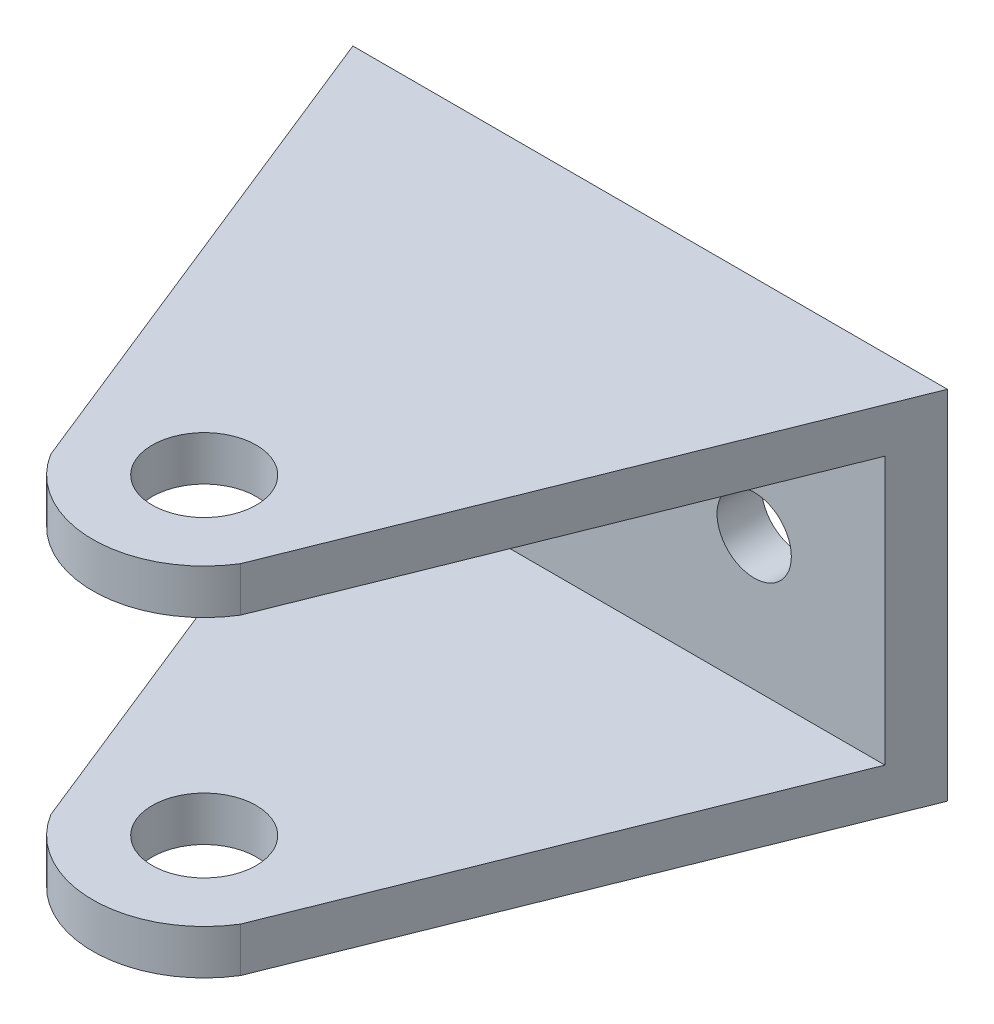
SolidWorks part; units mm, degrees
ref_plane "前视基准面" through (0, 0, 0) normal (0, 0, 1) x (1, 0, 0)
ref_plane "上视基准面" through (0, 0, 0) normal (0, 1, 0) x (1, 0, 0)
ref_plane "右视基准面" through (0, 0, 0) normal (1, 0, 0) x (0, 0, -1)
sketch "草图1" plane through (0, 0, 0) normal (0, 0, 1) x (1, 0, 0)
  line L0 (-29.7727, 16.3946) -> (-29.7727, -7.6054)
  line L1 (-29.7727, -7.6054) -> (0.2273, -7.6054)
  line L2 (0.2273, -7.6054) -> (10.2273, -7.6054)
  line L3 (10.2273, -7.6054) -> (10.2273, 16.3946)
  line L4 (-29.7727, 16.3946) -> (10.2273, 16.3946)
  line L5 (-29.7727, 4.3946) -> (-19.7727, 4.3946) construction
  line L6 (10.2273, 4.3946) -> (0.2273, 4.3946) construction
  circle A0 centre (-19.7727, 4.3946) radius 2.5
  circle A1 centre (0.2273, 4.3946) radius 2.5
  dimension "D5" = 5
  dimension "D6" = 10
  dimension "D7" = 5
  dimension "D1" = 24
  dimension "D2" = 30
  dimension "D3" = 10
  dimension "D4" = 10
extrude "凸台-拉伸1" add sketch "草图1" along normal blind 3
sketch "草图2" plane through (0, 0, 3) normal (0, 0, 1) x (1, 0, 0)
  line L0 (-29.7727, -7.6054) -> (-29.7727, -4.6054)
  line L1 (-29.7727, 16.3946) -> (-29.7727, -7.6054) construction
  line L2 (-29.7727, -4.6054) -> (10.2273, -4.6054)
  line L3 (10.2273, -7.6054) -> (10.2273, 16.3946) construction
  line L4 (10.2273, -4.6054) -> (10.2273, -7.6054)
  line L5 (10.2273, -7.6054) -> (-29.7727, -7.6054)
  line L6 (-29.7727, 16.3946) -> (-29.7727, 13.3946)
  line L7 (-29.7727, 13.3946) -> (10.2273, 13.3946)
  line L8 (10.2273, 13.3946) -> (10.2273, 16.3946)
  line L9 (10.2273, 16.3946) -> (-29.7727, 16.3946)
  dimension "D1" = 3
  dimension "D2" = 3
extrude "凸台-拉伸2" add sketch "草图2" along normal blind 40
sketch "草图3" plane through (0, -7.6054, 0) normal (0, -1, 0) x (1, 0, 0)
  line L0 (-9.7727, 0) -> (-9.7727, 30) construction
  line L1 (-29.7727, 0) -> (10.2273, 0) construction
  line L2 (-9.7727, 30) -> (-9.7727, 35) construction
  line L5 (-29.7727, 0) -> (-66.2428, 33.9385)
  line L6 (-66.2428, 33.9385) -> (4.75, 60.9912)
  line L7 (4.75, 60.9912) -> (36.3879, 40.2817)
  line L8 (36.3879, 40.2817) -> (10.2273, 0)
  line L9 (-29.7727, 0) -> (-16.1553, 33.9385)
  line L10 (10.2273, 0) -> (-3.3901, 33.9385)
  circle A1 centre (-9.7727, 30) radius 3.5
  arc A2 (-3.3901, 33.9385) -> (-16.1553, 33.9385) centre (-9.7727, 30) ccw
  dimension "D3" = 7
  dimension "D4" = 15
  dimension "D1" = 30
  dimension "D2" = 5
extrude "切除-拉伸1" cut sketch "草图3" against normal blind 40
